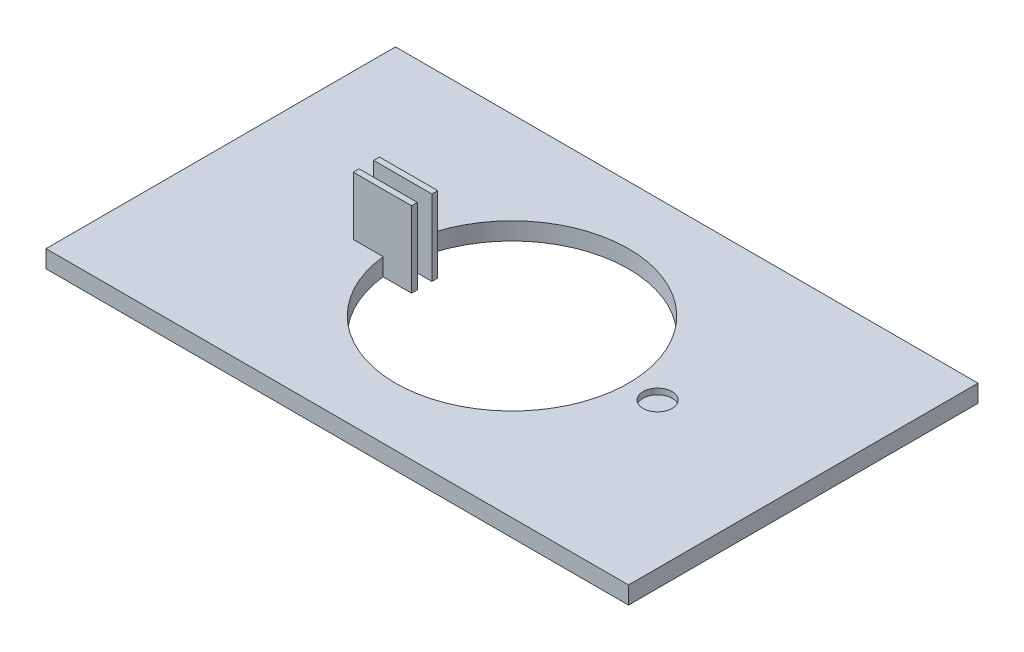
SolidWorks part; units mm, degrees
ref_plane "Alzado" through (0, 0, 0) normal (0, 0, 1) x (1, 0, 0)
ref_plane "Planta" through (0, 0, 0) normal (0, 1, 0) x (1, 0, 0)
ref_plane "Vista lateral" through (0, 0, 0) normal (1, 0, 0) x (0, 0, -1)
sketch "Croquis1" plane through (0, 0, 0) normal (0, 1, 0) x (1, 0, 0)
  line L1 (-50, 30) -> (50, 30)
  line L2 (-50, 30) -> (-50, -30)
  line L3 (-50, -30) -> (50, -30)
  line L4 (50, 30) -> (50, -30)
  line L5 (-50, 30) -> (50, -30) construction
  line L6 (-50, -30) -> (50, 30) construction
  circle A0 centre (0, 0) radius 20
  point P0 (0, 0)
  dimension "D1" = 40
  dimension "D2" = 60
  dimension "D3" = 100
extrude "Saliente-Extruir1" add sketch "Croquis1" along normal blind 3
sketch "Croquis2" plane through (0, 3, 0) normal (0, 1, 0) x (1, 0, 0)
  line L0 (0, 0) -> (-25, 0) construction
  line L1 (-25, 1.25) -> (-15, 1.25)
  line L2 (-15, 1.25) -> (-15, 2.25)
  line L3 (-15, 2.25) -> (-25, 2.25)
  line L4 (-25, 2.25) -> (-25, 1.25)
  line L5 (-25, -1.25) -> (-25, -2.25)
  line L6 (-25, -2.25) -> (-15, -2.25)
  line L7 (-15, -2.25) -> (-15, -1.25)
  line L8 (-15, -1.25) -> (-25, -1.25)
  line L9 (-20, -1.25) -> (-20, 0) construction
  line L10 (-20, 0) -> (-20, 1.25) construction
  dimension "D1" = 1
  dimension "D2" = 2.5
  dimension "D3" = 10
  dimension "D4" = 25
extrude "Saliente-Extruir2" add sketch "Croquis2" along normal blind 10 and the other way up to surface (3 mm away) other way up to face at (0, 0, 0)
sketch "Croquis3" plane through (0, 3, 0) normal (0, 1, 0) x (1, 0, 0)
  line L0 (0, 0) -> (12.5, 0) construction
  line L1 (12.5, 0) -> (25, 0) construction
  circle A1 centre (25, 0) radius 2.5
  dimension "D2" = 5
  dimension "D1" = 12.5
  dimension "D3" = 12.5
extrude "Cortar-Extruir1" cut sketch "Croquis3" against normal blind 1
